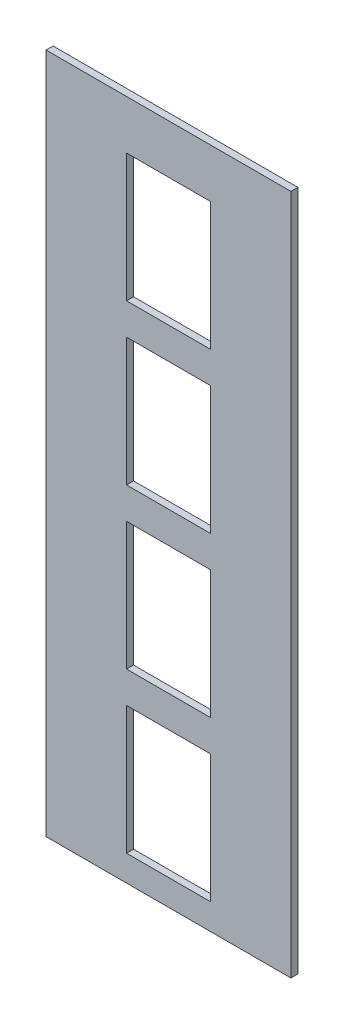
SolidWorks part; units mm, degrees
ref_plane "Front Plane" through (0, 0, 0) normal (0, 0, 1) x (1, 0, 0)
ref_plane "Top Plane" through (0, 0, 0) normal (0, 1, 0) x (1, 0, 0)
ref_plane "Right Plane" through (0, 0, 0) normal (1, 0, 0) x (0, 0, -1)
sketch "Sketch1" plane through (0, 0, 0) normal (0, 0, 1) x (1, 0, 0)
  line L0 (170, 128.5) -> (170, 974) construction
  line L7 (110, 37) -> (230, 37)
  line L8 (110, 37) -> (110, 220)
  line L9 (110, 220) -> (230, 220)
  line L10 (230, 37) -> (230, 220)
  line L11 (110, 37) -> (230, 220) construction
  line L12 (110, 220) -> (230, 37) construction
  line L32 (0, 0) -> (240, 0)
  line L33 (0, 0) -> (0, 974)
  line L34 (0, 974) -> (240, 974)
  line L35 (240, 0) -> (240, 974)
  line L36 (110, 265) -> (110, 448)
  line L37 (110, 265) -> (230, 265)
  line L38 (230, 265) -> (230, 448)
  line L39 (110, 448) -> (230, 448)
  line L40 (110, 493) -> (110, 676)
  line L41 (110, 493) -> (230, 493)
  line L42 (230, 493) -> (230, 676)
  line L43 (110, 676) -> (230, 676)
  line L44 (110, 721) -> (110, 904)
  line L45 (110, 721) -> (230, 721)
  line L46 (230, 721) -> (230, 904)
  line L47 (110, 904) -> (230, 904)
  point P0 (0, 0)
  point P6 (0, -130.75)
  dimension "D1" = 4
  dimension "D2" = 240
  dimension "D3" = 10
  dimension "D4" = 120
  dimension "D5" = 37
  dimension "D6" = 183
  dimension "D7" = 45
  dimension "D8" = 0
  dimension "D9" = 70
extrude "Boss-Extrude1" add sketch "Sketch1" along normal blind 10
sketch "Sketch2" plane through (0, 0, 0) normal (0, 0, 1) x (1, 0, 0)
  line L0 (240, 0) -> (240, 974) construction
other "Move Face1" face at (0, 487, 5) parameters "D1"=5
other "Move Face2" face at (240, 487, 5) parameters "D1"=105
